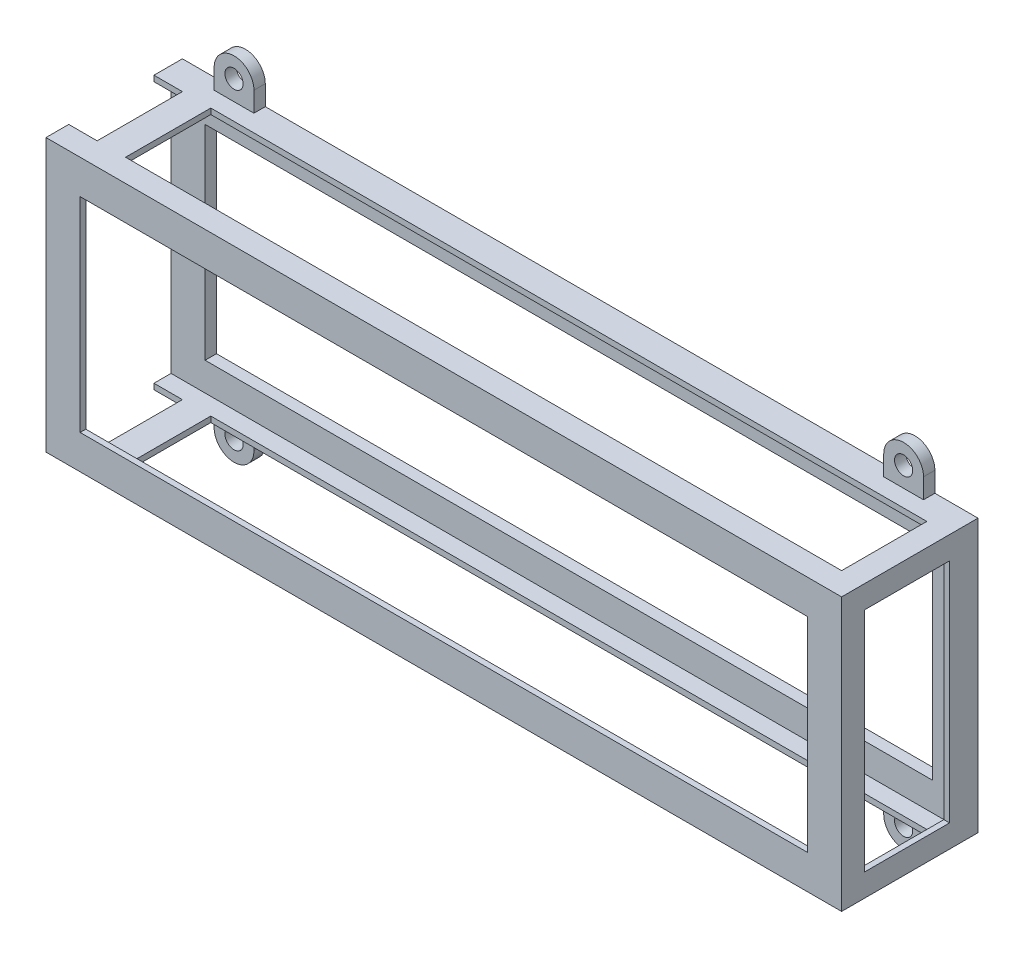
SolidWorks part; units mm, degrees
ref_plane "Front Plane" through (0, 0, 0) normal (0, 0, 1) x (1, 0, 0)
ref_plane "Top Plane" through (0, 0, 0) normal (0, 1, 0) x (1, 0, 0)
ref_plane "Right Plane" through (0, 0, 0) normal (1, 0, 0) x (0, 0, -1)
sketch "Sketch1" plane through (0, 0, 0) normal (0, 0, 1) x (1, 0, 0)
  line L1 (0, 0) -> (0, 3.5)
  line L4 (0, 0) -> (0, 54.9422)
  line L5 (0, 3.5) -> (37.9119, 3.5)
  line L6 (79.9119, 40.9711) -> (79.9119, 13.9711)
  line L7 (0, 51.4422) -> (37.9119, 51.4422)
  line L9 (45.9119, 51.4422) -> (45.9119, 58.4422)
  line L10 (117.8238, 58.4422) -> (71.9119, 58.4422)
  line L11 (66.9119, 5.9711) -> (71.9119, 5.9711)
  line L12 (71.9119, 5.9711) -> (71.9119, 3.5)
  line L13 (117.8238, -3.5) -> (71.9119, -3.5)
  line L15 (66.9119, 40.9711) -> (50.9119, 40.9711)
  line L17 (66.9119, 48.9711) -> (50.9119, 48.9711)
  line L18 (66.9119, 13.9711) -> (50.9119, 13.9711)
  line L19 (66.9119, 5.9711) -> (50.9119, 5.9711)
  line L22 (71.9119, 27.4711) -> (71.9119, 40.9711)
  line L23 (66.9119, 13.9711) -> (71.9119, 13.9711)
  line L24 (79.9119, 13.9711) -> (79.9119, 3.5)
  line L25 (71.9119, 3.5) -> (71.9119, -3.5)
  line L26 (79.9119, 3.5) -> (117.8238, 3.5)
  line L27 (71.9119, 27.4711) -> (71.9119, 13.9711)
  line L28 (50.9119, 5.9711) -> (45.9119, 5.9711)
  line L29 (45.9119, 5.9711) -> (45.9119, 3.5)
  line L30 (50.9119, 13.9711) -> (45.9119, 13.9711)
  line L31 (37.9119, 13.9711) -> (37.9119, 3.5)
  line L32 (79.9119, 40.9711) -> (79.9119, 51.4422)
  line L33 (66.9119, 40.9711) -> (71.9119, 40.9711)
  line L34 (66.9119, 48.9711) -> (71.9119, 48.9711)
  line L35 (71.9119, 48.9711) -> (71.9119, 51.4422)
  line L36 (50.9119, 48.9711) -> (45.9119, 48.9711)
  line L37 (45.9119, 48.9711) -> (45.9119, 51.4422)
  line L38 (37.9119, 40.9711) -> (37.9119, 51.4422)
  line L39 (50.9119, 40.9711) -> (45.9119, 40.9711)
  line L41 (45.9119, 3.5) -> (45.9119, -3.5)
  line L42 (45.9119, -3.5) -> (0, -3.5)
  line L43 (71.9119, 51.4422) -> (71.9119, 58.4422)
  line L44 (45.9119, 58.4422) -> (0, 58.4422)
  line L45 (79.9119, 51.4422) -> (117.8238, 51.4422)
  line L46 (37.9119, 40.9711) -> (37.9119, 13.9711)
  line L48 (45.9119, 27.4711) -> (45.9119, 40.9711)
  line L49 (45.9119, 27.4711) -> (45.9119, 13.9711)
  circle A0 centre (0, 54.9422) radius 1.6
  circle A1 centre (117.8238, 54.9422) radius 1.6
  circle A2 centre (117.8238, 0) radius 1.6
  circle A3 centre (0, 0) radius 1.6
  arc A4 (0, 58.4422) -> (0, 51.4422) centre (0, 54.9422) ccw
  arc A5 (117.8238, 51.4422) -> (117.8238, 58.4422) centre (117.8238, 54.9422) ccw
  arc A6 (117.8238, -3.5) -> (117.8238, 3.5) centre (117.8238, 0) ccw
  arc A7 (0, 3.5) -> (0, -3.5) centre (0, 0) ccw
  circle A8 centre (66.9119, 44.9711) radius 2.1
  circle A9 centre (66.9119, 9.9711) radius 2.1
  circle A14 centre (50.9119, 9.9711) radius 2.1
  circle A15 centre (50.9119, 44.9711) radius 2.1
  point P32 (58.9119, 40.9711)
  point P34 (58.9119, 48.9711)
  point P36 (58.9119, 13.9711)
  point P41 (58.9119, 5.9711)
  dimension "D1" = 54.9422
  dimension "D2" = 3.5
  dimension "D3" = 117.8238
extrude "Boss-Extrude3" add sketch "Sketch1" along normal blind 2
sketch "Sketch3" plane through (0, 0, 2) normal (0, 0, 1) x (1, 0, 0)
  line L0 (71.9119, 13.9711) -> (99.9119, 13.9711)
  line L1 (99.9119, 13.9711) -> (99.9119, 3.5)
  line L2 (79.9119, 3.5) -> (117.8238, 3.5) construction
  line L3 (71.9119, 13.9711) -> (71.9119, 5.9711)
  line L4 (71.9119, 5.9711) -> (91.9119, 5.9711)
  line L5 (91.9119, 5.9711) -> (91.9119, 3.5)
  line L6 (91.9119, 3.5) -> (99.9119, 3.5)
  line L12 (91.9119, 51.4422) -> (99.9119, 51.4422)
  line L13 (91.9119, 48.9711) -> (91.9119, 51.4422)
  line L14 (71.9119, 48.9711) -> (91.9119, 48.9711)
  line L15 (71.9119, 40.9711) -> (71.9119, 48.9711)
  line L16 (99.9119, 40.9711) -> (99.9119, 51.4422)
  line L17 (71.9119, 40.9711) -> (99.9119, 40.9711)
  line L18 (45.9119, 40.9711) -> (17.9119, 40.9711)
  line L19 (17.9119, 40.9711) -> (17.9119, 51.4422)
  line L20 (45.9119, 40.9711) -> (45.9119, 48.9711)
  line L21 (45.9119, 48.9711) -> (25.9119, 48.9711)
  line L22 (25.9119, 48.9711) -> (25.9119, 51.4422)
  line L23 (25.9119, 51.4422) -> (17.9119, 51.4422)
  line L24 (25.9119, 3.5) -> (17.9119, 3.5)
  line L25 (25.9119, 5.9711) -> (25.9119, 3.5)
  line L26 (45.9119, 5.9711) -> (25.9119, 5.9711)
  line L27 (45.9119, 13.9711) -> (45.9119, 5.9711)
  line L28 (17.9119, 13.9711) -> (17.9119, 3.5)
  line L29 (45.9119, 13.9711) -> (17.9119, 13.9711)
extrude "Boss-Extrude4" add sketch "Sketch3" against normal up to surface (2 mm away) up to face at (58.9119, 27.4711, 0)
sketch "Sketch4" plane through (0, 0, 2) normal (0, 0, 1) x (1, 0, 0)
  line L0 (25.9119, 48.9711) -> (25.9119, 65.3112)
  line L1 (25.9119, 48.9711) -> (91.9119, 48.9711)
  line L2 (91.9119, 48.9711) -> (91.9119, 65.3112)
  line L3 (91.9119, 65.3112) -> (25.9119, 65.3112)
  line L4 (25.9119, 5.9711) -> (91.9119, 5.9711)
  line L5 (91.9119, 5.9711) -> (91.9119, -18.7705)
  line L6 (91.9119, -18.7705) -> (25.9119, -18.7705)
  line L7 (25.9119, -18.7705) -> (25.9119, 5.9711)
extrude "Cut-Extrude3" cut sketch "Sketch4" against normal blind 14.5
fillet "Fillet1" radius 4 16 edges at (25.9119, 48.9711, 1) (25.9119, 58.4422, 1) (17.9119, 51.4422, 1) (17.9119, 40.9711, 1) (25.9119, 5.9711, 1) (25.9119, -3.5, 1) (17.9119, 3.5, 1) (17.9119, 13.9711, 1) (99.9119, 13.9711, 1) (99.9119, 3.5, 1) (91.9119, 5.9711, 1) (91.9119, -3.5, 1) (99.9119, 40.9711, 1) (99.9119, 51.4422, 1) (91.9119, 48.9711, 1) (91.9119, 58.4422, 1)
sketch "Sketch5" plane through (0, 0, 2) normal (0, 0, 1) x (1, 0, 0)
  line L0 (45.9119, 40.9711) -> (45.9119, 13.9711)
  line L3 (45.9119, 13.9711) -> (71.9119, 13.9711)
  line L5 (71.9119, 13.9711) -> (71.9119, 40.9711)
  line L6 (71.9119, 40.9711) -> (45.9119, 40.9711)
  circle A0 centre (58.9119, 27.4711) radius 6
extrude "Boss-Extrude5" add sketch "Sketch5" against normal up to surface (2 mm away) up to face at (58.9119, 27.4711, 0)
sketch "Sketch6" plane through (0, 0, 2) normal (0, 0, 1) x (1, 0, 0)
  line L0 (37.9119, 40.9711) -> (42.9119, 40.9711)
  line L1 (37.9119, 13.9711) -> (42.9119, 13.9711)
  line L2 (42.9119, 13.9711) -> (42.9119, 40.9711)
  line L3 (37.9119, 40.9711) -> (37.9119, 13.9711)
  line L4 (79.9119, 13.9711) -> (74.9119, 13.9711)
  line L5 (74.9119, 13.9711) -> (74.9119, 40.9711)
  line L6 (74.9119, 40.9711) -> (79.9119, 40.9711)
  line L7 (79.9119, 40.9711) -> (79.9119, 13.9711)
extrude "Cut-Extrude4" cut sketch "Sketch6" against normal blind 14.5
sketch "Sketch7" plane through (0, 0, 2) normal (0, 0, 1) x (1, 0, 0)
  line L0 (-3.5, 54.9422) -> (-3.5, 0)
  line L1 (0, 58.4422) -> (117.8238, 58.4422)
  line L2 (121.3238, 54.9422) -> (121.3238, 0)
  line L3 (117.8238, -3.5) -> (0, -3.5)
  line L4 (3.5, 51.4422) -> (3.5, 3.5)
  line L5 (114.3238, 51.4422) -> (114.3238, 3.5)
  line L6 (3.5, 51.4422) -> (114.3238, 51.4422)
  line L7 (114.3238, 3.5) -> (3.5, 3.5)
  arc A0 (0, 58.4422) -> (-3.5, 54.9422) centre (0, 54.9422) ccw
  arc A1 (-3.5, 0) -> (0, -3.5) centre (0, 0) ccw
  arc A2 (121.3238, 54.9422) -> (117.8238, 58.4422) centre (117.8238, 54.9422) ccw
  arc A3 (117.8238, -3.5) -> (121.3238, 0) centre (117.8238, 0) ccw
  circle A4 centre (0, 0) radius 1.6
  circle A5 centre (117.8238, 0) radius 1.6
  circle A6 centre (117.8238, 54.9422) radius 1.6
  circle A7 centre (0, 54.9422) radius 1.6
extrude "Boss-Extrude6" add sketch "Sketch7" against normal up to surface (2 mm away) up to face at (1.6, 0, 0)
sketch "Sketch8" plane through (0, 0, 2) normal (0, 0, 1) x (1, 0, 0)
  line L0 (3.5, 51.4422) -> (3.5, 3.5)
  line L1 (3.5, 3.5) -> (114.3238, 3.5)
  line L2 (114.3238, 3.5) -> (114.3238, 51.4422)
  line L3 (114.3238, 51.4422) -> (3.5, 51.4422)
extrude "Cut-Extrude5" cut sketch "Sketch8" against normal blind 10
sketch "Sketch9" plane through (0, 0, 2) normal (0, 0, 1) x (1, 0, 0)
  line L5 (58.9119, 51.4422) -> (128.9119, 51.4422)
  line L6 (3.5, 51.4422) -> (114.3238, 51.4422) construction
  line L7 (128.9119, 51.4422) -> (128.9119, 3.5)
  line L8 (128.9119, 3.5) -> (-11.0881, 3.5)
  line L9 (-11.0881, 3.5) -> (-11.0881, 51.4422)
  line L10 (-11.0881, 51.4422) -> (58.9119, 51.4422)
extrude "Boss-Extrude7" add sketch "Sketch9" against normal up to surface (2 mm away) up to face at (58.9119, 27.4711, 0)
sketch "Sketch10" plane through (0, 0, 2) normal (0, 0, 1) x (1, 0, 0)
  line L0 (-11.0881, 51.4422) -> (128.9119, 51.4422)
  line L1 (128.9119, 51.4422) -> (128.9119, 3.5)
  line L2 (128.9119, 3.5) -> (-11.0881, 3.5)
  line L3 (-11.0881, 3.5) -> (-11.0881, 4.5)
  line L4 (-11.0881, 51.4422) -> (-11.0881, 3.5) construction
  line L6 (127.9119, 27.4711) -> (127.9119, 4.5)
  line L7 (127.9119, 4.5) -> (-11.0881, 4.5)
  line L8 (-11.0881, 51.4422) -> (-11.0881, 50.4422)
  line L9 (-11.0881, 50.4422) -> (127.9119, 50.4422)
  line L10 (127.9119, 50.4422) -> (127.9119, 27.4711)
extrude "Boss-Extrude8" add sketch "Sketch10" along normal blind 21
sketch "Sketch11" plane through (0, 0, 23) normal (0, 0, 1) x (1, 0, 0)
  line L0 (-11.0881, 51.4422) -> (-11.0881, 3.5)
  line L1 (-11.0881, 3.5) -> (128.9119, 3.5)
  line L2 (128.9119, 3.5) -> (128.9119, 51.4422)
  line L3 (128.9119, 51.4422) -> (-11.0881, 51.4422)
extrude "Boss-Extrude9" add sketch "Sketch11" along normal blind 1
sketch "Sketch12" plane through (0, 0, 2) normal (0, 0, 1) x (1, 0, 0)
  line L0 (3.5, 0) -> (3.5, 3.5)
  line L1 (-11.0881, 3.5) -> (128.9119, 3.5) construction
  line L3 (114.3238, 0) -> (114.3238, 3.5)
  line L4 (114.3238, 3.5) -> (3.5, 3.5)
  line L5 (3.5, 54.9422) -> (3.5, 51.4422)
  line L6 (121.3238, 51.4422) -> (-3.5, 51.4422) construction
  line L8 (114.3238, 54.9422) -> (114.3238, 51.4422)
  line L9 (128.9119, 51.4422) -> (-11.0881, 51.4422) construction
  line L10 (114.3238, 51.4422) -> (3.5, 51.4422)
  line L11 (0, 58.4422) -> (117.8238, 58.4422)
  line L13 (117.8238, -3.5) -> (0, -3.5)
  arc A0 (0, -3.5) -> (3.5, 0) centre (0, 0) ccw
  arc A1 (3.5, 54.9422) -> (0, 58.4422) centre (0, 54.9422) ccw
  arc A2 (117.8238, 58.4422) -> (114.3238, 54.9422) centre (117.8238, 54.9422) ccw
  arc A3 (114.3238, 0) -> (117.8238, -3.5) centre (117.8238, 0) ccw
extrude "Cut-Extrude7" cut sketch "Sketch12" against normal blind 13
sketch "Sketch13" plane through (128.9119, 0, 0) normal (1, 0, 0) x (0, 0, -1)
  line L8 (-20, 27.4711) -> (-20, 47.4422)
  line L9 (-20, 47.4422) -> (-5, 47.4422)
  line L10 (-5, 47.4422) -> (-5, 7.5)
  line L11 (-5, 7.5) -> (-20, 7.5)
  line L12 (-20, 7.5) -> (-20, 27.4711)
extrude "Cut-Extrude8" cut sketch "Sketch13" against normal blind 13
sketch "Sketch14" plane through (0, 0, 0) normal (0, 0, -1) x (-1, 0, 0)
  line L8 (-58.9119, 9.5) -> (-122.9119, 9.5)
  line L9 (-122.9119, 9.5) -> (-122.9119, 45.4422)
  line L10 (-122.9119, 45.4422) -> (5.0881, 45.4422)
  line L11 (5.0881, 45.4422) -> (5.0881, 9.5)
  line L12 (5.0881, 9.5) -> (-58.9119, 9.5)
extrude "Cut-Extrude9" cut sketch "Sketch14" against normal blind 66
sketch "Sketch15" plane through (0, 51.4422, 0) normal (0, 1, 0) x (1, 0, 0)
  line L4 (-1.0881, -12) -> (-1.0881, -5)
  line L6 (-1.0881, -5) -> (-1.0881, -20)
  line L8 (58.9119, -5) -> (-1.0881, -5)
  line L10 (-1.0881, -20) -> (124.9119, -20)
  line L11 (124.9119, -20) -> (124.9119, -5)
  line L12 (124.9119, -5) -> (58.9119, -5)
extrude "Cut-Extrude11" cut sketch "Sketch15" against normal blind 66 contours L11 L12 L8 L4 L6 L10
sketch "Sketch16" plane through (0, 51.4422, 0) normal (0, 1, 0) x (1, 0, 0)
  line L0 (-6.0881, -5) -> (-11.0881, -5)
  line L1 (-11.0881, 0) -> (-11.0881, -24) construction
  line L3 (-6.0881, -20) -> (-11.0881, -20)
  line L4 (-6.0881, -12) -> (-6.0881, -5)
  line L5 (-6.0881, -5) -> (-6.0881, -20)
  line L6 (-6.0881, -20) -> (-11.0881, -20)
  line L7 (-11.0881, -5) -> (-11.0881, -20)
  line M5 (-11.0881, 0) -> (-11.0881, -24)
extrude "Cut-Extrude12" cut sketch "Sketch16" against normal blind 66 contours L5 L4 L0 L3 M5
